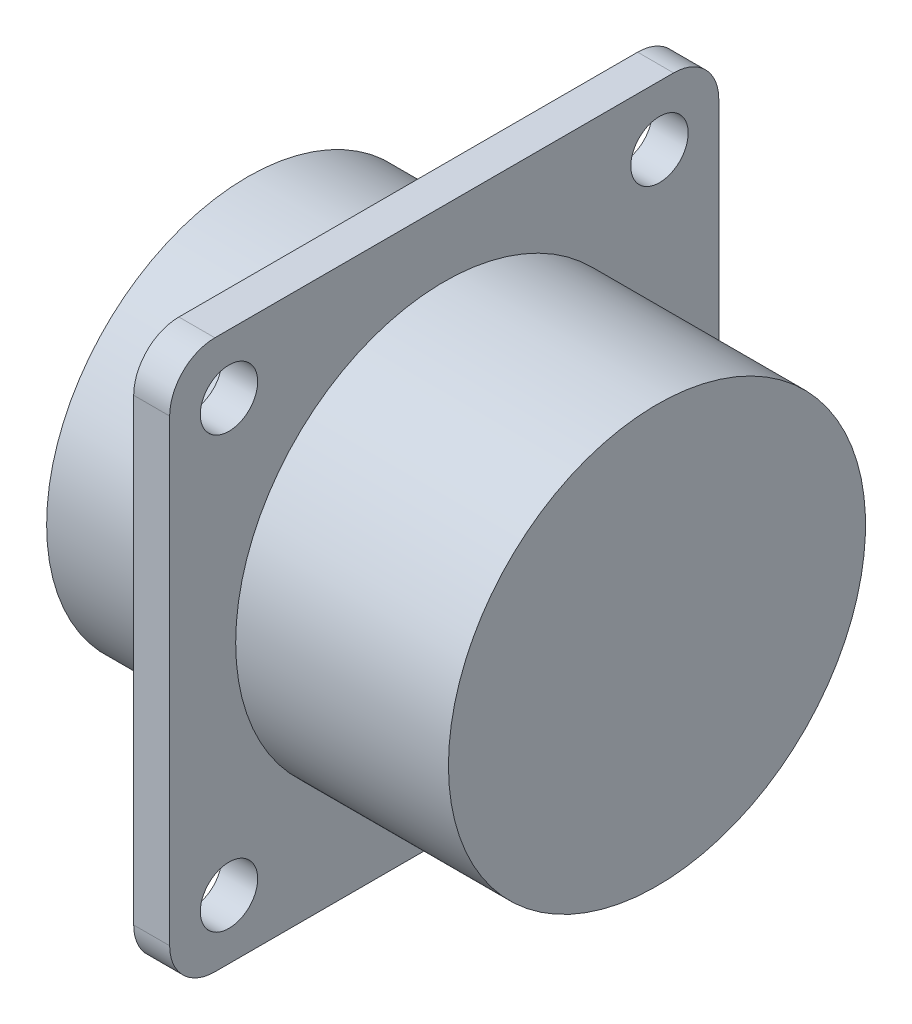
SolidWorks part; units mm, degrees
ref_plane "Front Plane" through (0, 0, 0) normal (0, 0, 1) x (1, 0, 0)
ref_plane "Top Plane" through (0, 0, 0) normal (0, 1, 0) x (1, 0, 0)
ref_plane "Right Plane" through (0, 0, 0) normal (1, 0, 0) x (0, 0, -1)
sketch "Sketch1" plane through (0, 0, 0) normal (0, 0, 1) x (1, 0, 0)
  line L0 (0, 0) -> (67.6328, 0) construction
  line L1 (0, 0) -> (0, 13.335)
  line L2 (0, 13.335) -> (10.668, 13.335)
  line L3 (10.668, 13.335) -> (10.668, 30)
  line L4 (10.668, 30) -> (13.0556, 30)
  line L5 (13.0556, 30) -> (13.0556, 13.843)
  line L6 (13.0556, 13.843) -> (27.178, 13.843)
  line L7 (27.178, 13.843) -> (27.178, 0)
  line L8 (27.178, 0) -> (0, 0)
  dimension "D1" = 2.3876
  dimension "D2" = 10.668
  dimension "D3" = 27.178
  dimension "D4" = 26.67
  dimension "D5" = 27.686
  dimension "D6" = 60
revolve "Revolve1" add sketch "Sketch1" angle 360 about L0
sketch "Sketch2" plane through (10.668, 0, 0) normal (-1, 0, 0) x (0, 0, 1)
  line L0 (-18.2245, 18.2245) -> (18.2245, -18.2245) construction
  line L1 (-15.2245, 18.2245) -> (15.2245, 18.2245)
  line L2 (-18.2245, 15.2245) -> (-18.2245, -15.2245)
  line L3 (-15.2245, -18.2245) -> (15.2245, -18.2245)
  line L4 (18.2245, 15.2245) -> (18.2245, -15.2245)
  line L5 (-14.2875, -14.2875) -> (14.2875, 14.2875) construction
  circle A0 centre (14.2875, 14.2875) radius 1.905
  circle A1 centre (-14.2875, 14.2875) radius 1.905
  circle A2 centre (-14.2875, -14.2875) radius 1.905
  circle A3 centre (14.2875, -14.2875) radius 1.905
  arc A4 (-18.2245, -15.2245) -> (-15.2245, -18.2245) centre (-15.2245, -15.2245) ccw
  arc A5 (15.2245, -18.2245) -> (18.2245, -15.2245) centre (15.2245, -15.2245) ccw
  arc A6 (15.2245, 18.2245) -> (18.2245, 15.2245) centre (15.2245, 15.2245) cw
  arc A7 (-15.2245, 18.2245) -> (-18.2245, 15.2245) centre (-15.2245, 15.2245) ccw
  point P20 (18.2245, 18.2245)
  dimension "D4" = 3.81
  dimension "D5" = 3
  dimension "D1" = 36.449
  dimension "D2" = 28.575
  dimension "D3" = 28.575
extrude "Cut-Extrude1" cut sketch "Sketch2" against normal through all flip side to cut
